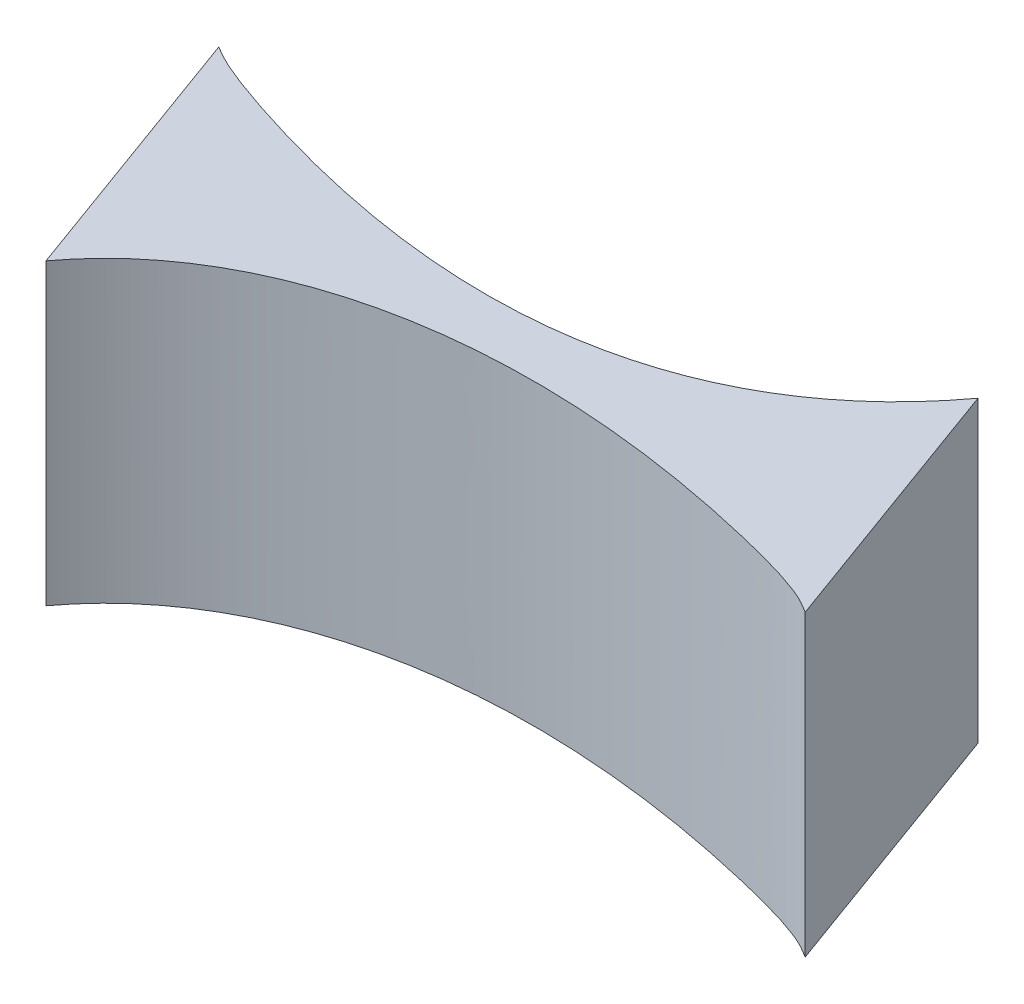
SolidWorks part; units mm, degrees
ref_plane "Front Plane" through (0, 0, 0) normal (0, 0, 1) x (1, 0, 0)
ref_plane "Top Plane" through (0, 0, 0) normal (0, 1, 0) x (1, 0, 0)
ref_plane "Right Plane" through (0, 0, 0) normal (1, 0, 0) x (0, 0, -1)
sketch "Sketch1" plane through (0, 0, 0) normal (0, 1, 0) x (1, 0, 0)
  line L2 (-4.7163, -52.391) -> (-14.9769, -24.2003)
  line L3 (66.252, -44.5657) -> (55.9914, -16.3749)
  spline S2 degree 3 poles (55.9914, -16.3749) (45.9589, -30.0089) (25.1941, -38.9229) (-12.7606, -25.6028) (-14.6054, -24.4118) (-14.9769, -24.2003) knots 0 0 0 0 0.403452 0.449137 0.45685 0.45685 0.45685 0.45685
  spline S3 degree 3 poles (-4.7163, -52.391) (5.3162, -38.7571) (29.9418, -33.5547) (63.9367, -43.0681) (65.8806, -44.3542) (66.252, -44.5657) knots 0 0 0 0 0.403452 0.449137 0.45685 0.45685 0.45685 0.45685
extrude "Boss-Extrude1" add sketch "Sketch1" along normal blind 31
